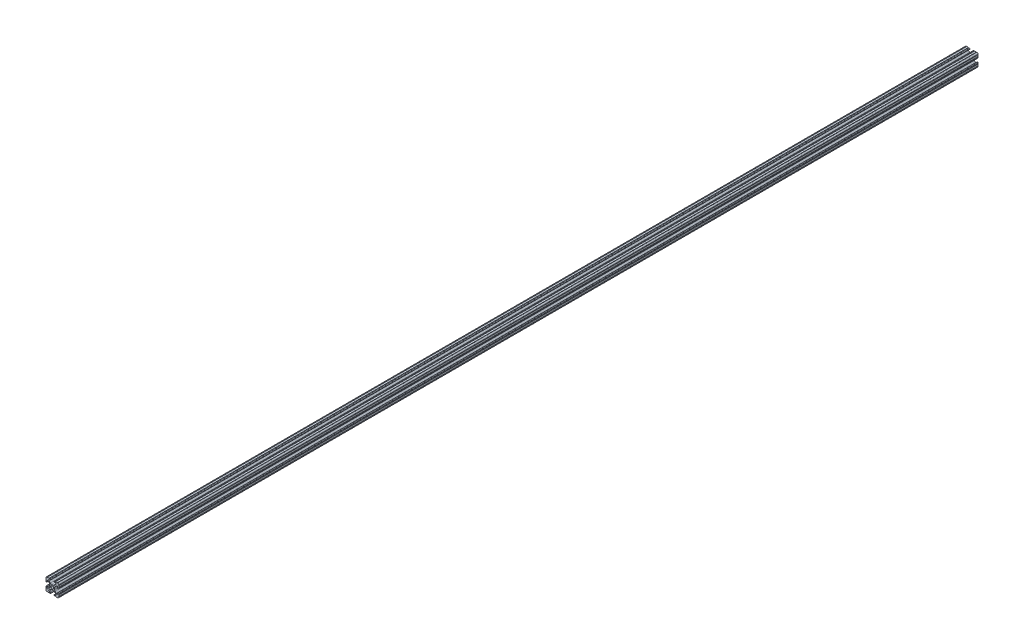
SolidWorks part; units mm, degrees
ref_plane "Front Plane" through (0, 0, 0) normal (0, 0, 1) x (1, 0, 0)
ref_plane "Top Plane" through (0, 0, 0) normal (0, 1, 0) x (1, 0, 0)
ref_plane "Right Plane" through (0, 0, 0) normal (1, 0, 0) x (0, 0, -1)
sketch "Sketch1" plane through (0, 0, 0) normal (0, 0, 1) x (1, 0, 0)
  line L88 (-7.1797, -8.6452) -> (-3.9523, -5.4237)
  line L89 (-1.7093, -4.4958) -> (1.7093, -4.4958)
  line L90 (3.9523, -5.4237) -> (7.1797, -8.6452)
  line L91 (6.4164, -10.4902) -> (4.2875, -10.4902)
  line L92 (3.2385, -11.5392) -> (3.2385, -11.651)
  line L93 (4.2875, -12.7) -> (5.3171, -12.7)
  line L94 (6.3331, -12.7) -> (9.5504, -12.7)
  line L95 (12.7, -9.5504) -> (12.7, -6.3331)
  line L96 (12.7, -5.3171) -> (12.7, -4.2875)
  line L97 (11.651, -3.2385) -> (11.5392, -3.2385)
  line L98 (10.4902, -4.2875) -> (10.4902, -6.4021)
  line L99 (8.7371, -7.1294) -> (5.441, -3.8408)
  line L100 (4.5085, -1.5932) -> (4.5085, 1.5932)
  line L101 (5.441, 3.8408) -> (8.7371, 7.1294)
  line L102 (10.4902, 6.4021) -> (10.4902, 4.2875)
  line L103 (11.5392, 3.2385) -> (11.651, 3.2385)
  line L104 (12.7, 4.2875) -> (12.7, 5.3171)
  line L105 (12.7, 6.3331) -> (12.7, 9.5504)
  line L106 (9.5504, 12.7) -> (6.3331, 12.7)
  line L107 (5.3171, 12.7) -> (4.2875, 12.7)
  line L108 (3.2385, 11.651) -> (3.2385, 11.5392)
  line L109 (4.2875, 10.4902) -> (6.4768, 10.4902)
  line L110 (7.207, 8.7244) -> (3.8983, 5.4232)
  line L111 (1.6558, 4.4958) -> (-1.6558, 4.4958)
  line L112 (-3.8983, 5.4232) -> (-7.207, 8.7244)
  line L113 (-6.4768, 10.4902) -> (-4.2875, 10.4902)
  line L114 (-3.2385, 11.5392) -> (-3.2385, 11.651)
  line L115 (-4.2875, 12.7) -> (-5.3171, 12.7)
  line L116 (-6.3331, 12.7) -> (-9.5504, 12.7)
  line L117 (-12.7, 9.5504) -> (-12.7, 6.3331)
  line L118 (-12.7, 5.3171) -> (-12.7, 4.2875)
  line L119 (-11.651, 3.2385) -> (-11.5392, 3.2385)
  line L120 (-10.4902, 4.2875) -> (-10.4902, 6.4021)
  line L121 (-8.7371, 7.1294) -> (-5.441, 3.8408)
  line L122 (-4.5085, 1.5932) -> (-4.5085, -1.5932)
  line L123 (-5.441, -3.8408) -> (-8.7371, -7.1294)
  line L124 (-10.4902, -6.4021) -> (-10.4902, -4.2875)
  line L125 (-11.5392, -3.2385) -> (-11.651, -3.2385)
  line L126 (-12.7, -4.2875) -> (-12.7, -5.3171)
  line L127 (-12.7, -6.3331) -> (-12.7, -9.5504)
  line L128 (-9.5504, -12.7) -> (-6.3331, -12.7)
  line L129 (-5.3171, -12.7) -> (-4.2875, -12.7)
  line L130 (-3.2385, -11.651) -> (-3.2385, -11.5392)
  line L131 (-4.2875, -10.4902) -> (-6.4164, -10.4902)
  circle A1 centre (0, 0) radius 2.6035
  arc A104 (-7.1797, -8.6452) -> (-6.4164, -10.4902) centre (-6.4164, -9.4098) ccw
  arc A105 (-1.7093, -4.4958) -> (-3.9523, -5.4237) centre (-1.7093, -7.6708) ccw
  arc A106 (3.9523, -5.4237) -> (1.7093, -4.4958) centre (1.7093, -7.6708) ccw
  arc A107 (6.4164, -10.4902) -> (7.1797, -8.6452) centre (6.4164, -9.4098) ccw
  arc A108 (4.2875, -10.4902) -> (3.2385, -11.5392) centre (4.2875, -11.5392) ccw
  arc A109 (3.2385, -11.651) -> (4.2875, -12.7) centre (4.2875, -11.651) ccw
  arc A110 (6.3331, -12.7) -> (5.3171, -12.7) centre (5.8251, -12.7) ccw
  arc A111 (10.5664, -12.6998) -> (9.5504, -12.7) centre (10.0584, -12.7) ccw
  arc A112 (10.5664, -12.6998) -> (12.6998, -10.5664) centre (10.5918, -10.5918) ccw
  arc A113 (12.7, -9.5504) -> (12.6998, -10.5664) centre (12.7, -10.0584) ccw
  arc A114 (12.7, -5.3171) -> (12.7, -6.3331) centre (12.7, -5.8251) ccw
  arc A115 (12.7, -4.2875) -> (11.651, -3.2385) centre (11.651, -4.2875) ccw
  arc A116 (11.5392, -3.2385) -> (10.4902, -4.2875) centre (11.5392, -4.2875) ccw
  arc A117 (8.7371, -7.1294) -> (10.4902, -6.4021) centre (9.4628, -6.4021) ccw
  arc A118 (4.5085, -1.5932) -> (5.441, -3.8408) centre (7.6835, -1.5932) ccw
  arc A119 (5.441, 3.8408) -> (4.5085, 1.5932) centre (7.6835, 1.5932) ccw
  arc A120 (10.4902, 6.4021) -> (8.7371, 7.1294) centre (9.4628, 6.4021) ccw
  arc A121 (10.4902, 4.2875) -> (11.5392, 3.2385) centre (11.5392, 4.2875) ccw
  arc A122 (11.651, 3.2385) -> (12.7, 4.2875) centre (11.651, 4.2875) ccw
  arc A123 (12.7, 6.3331) -> (12.7, 5.3171) centre (12.7, 5.8251) ccw
  arc A124 (12.6998, 10.5664) -> (12.7, 9.5504) centre (12.7, 10.0584) ccw
  arc A125 (12.6998, 10.5664) -> (10.5664, 12.6998) centre (10.5918, 10.5918) ccw
  arc A126 (9.5504, 12.7) -> (10.5664, 12.6998) centre (10.0584, 12.7) ccw
  arc A127 (5.3171, 12.7) -> (6.3331, 12.7) centre (5.8251, 12.7) ccw
  arc A128 (4.2875, 12.7) -> (3.2385, 11.651) centre (4.2875, 11.651) ccw
  arc A129 (3.2385, 11.5392) -> (4.2875, 10.4902) centre (4.2875, 11.5392) ccw
  arc A130 (7.207, 8.7244) -> (6.4768, 10.4902) centre (6.4768, 9.4563) ccw
  arc A131 (1.6558, 4.4958) -> (3.8983, 5.4232) centre (1.6558, 7.6708) ccw
  arc A132 (-3.8983, 5.4232) -> (-1.6558, 4.4958) centre (-1.6558, 7.6708) ccw
  arc A133 (-6.4768, 10.4902) -> (-7.207, 8.7244) centre (-6.4768, 9.4563) ccw
  arc A134 (-4.2875, 10.4902) -> (-3.2385, 11.5392) centre (-4.2875, 11.5392) ccw
  arc A135 (-3.2385, 11.651) -> (-4.2875, 12.7) centre (-4.2875, 11.651) ccw
  arc A136 (-6.3331, 12.7) -> (-5.3171, 12.7) centre (-5.8251, 12.7) ccw
  arc A137 (-10.5664, 12.6998) -> (-9.5504, 12.7) centre (-10.0584, 12.7) ccw
  arc A138 (-10.5664, 12.6998) -> (-12.6998, 10.5664) centre (-10.5918, 10.5918) ccw
  arc A139 (-12.7, 9.5504) -> (-12.6998, 10.5664) centre (-12.7, 10.0584) ccw
  arc A140 (-12.7, 5.3171) -> (-12.7, 6.3331) centre (-12.7, 5.8251) ccw
  arc A141 (-12.7, 4.2875) -> (-11.651, 3.2385) centre (-11.651, 4.2875) ccw
  arc A142 (-11.5392, 3.2385) -> (-10.4902, 4.2875) centre (-11.5392, 4.2875) ccw
  arc A143 (-8.7371, 7.1294) -> (-10.4902, 6.4021) centre (-9.4628, 6.4021) ccw
  arc A144 (-4.5085, 1.5932) -> (-5.441, 3.8408) centre (-7.6835, 1.5932) ccw
  arc A145 (-5.441, -3.8408) -> (-4.5085, -1.5932) centre (-7.6835, -1.5932) ccw
  arc A146 (-10.4902, -6.4021) -> (-8.7371, -7.1294) centre (-9.4628, -6.4021) ccw
  arc A147 (-10.4902, -4.2875) -> (-11.5392, -3.2385) centre (-11.5392, -4.2875) ccw
  arc A148 (-11.651, -3.2385) -> (-12.7, -4.2875) centre (-11.651, -4.2875) ccw
  arc A149 (-12.7, -6.3331) -> (-12.7, -5.3171) centre (-12.7, -5.8251) ccw
  arc A150 (-12.6998, -10.5664) -> (-12.7, -9.5504) centre (-12.7, -10.0584) ccw
  arc A151 (-12.6998, -10.5664) -> (-10.5664, -12.6998) centre (-10.5918, -10.5918) ccw
  arc A152 (-9.5504, -12.7) -> (-10.5664, -12.6998) centre (-10.0584, -12.7) ccw
  arc A153 (-5.3171, -12.7) -> (-6.3331, -12.7) centre (-5.8251, -12.7) ccw
  arc A154 (-4.2875, -12.7) -> (-3.2385, -11.651) centre (-4.2875, -11.651) ccw
  arc A155 (-3.2385, -11.5392) -> (-4.2875, -10.4902) centre (-4.2875, -11.5392) ccw
extrude "Boss-Extrude1" add sketch "Sketch1" along normal mid plane 1828.8
sketch "Sketch2" plane through (4.5085, 0, 0) normal (1, 0, 0) x (0, 0, -1)
  line L0 (-914.4, -1.5932) -> (-914.4, 1.5932) construction
  circle A0 centre (0, 0) radius 3.175
  circle A1 centre (76.2, 0) radius 3.175
  circle A2 centre (-76.2, 0) radius 3.175
  dimension "D1" = 6.35
  dimension "D2" = 914.4
  dimension "D3" = 6.35
  dimension "D4" = 6.35
  dimension "D5" = 76.2
  dimension "D6" = 76.2
extrude "Cut-Extrude1" cut sketch "Sketch2" against normal through all and the other way through all
sketch "Sketch3" plane through (0, 4.4958, 0) normal (0, 1, 0) x (1, 0, 0)
  line L0 (1.6558, -914.4) -> (-1.6558, -914.4) construction
  line L1 (1.6558, 914.4) -> (-1.6558, 914.4) construction
  circle A0 centre (0, -901.7) radius 3.175
  circle A1 centre (0, 901.7) radius 3.175
  dimension "D1" = 6.35
  dimension "D3" = 6.35
  dimension "D2" = 12.7
  dimension "D4" = 12.7
extrude "Cut-Extrude2" cut sketch "Sketch3" against normal through all both and the other way through all
